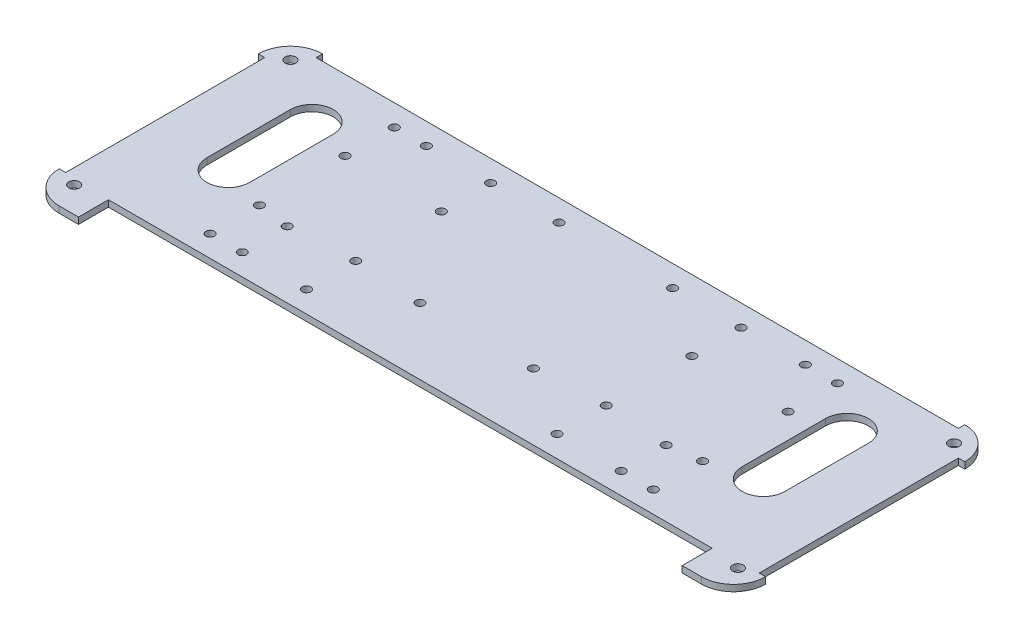
SolidWorks part; units mm, degrees
ref_plane "Plan de face" through (0, 0, 0) normal (0, 0, 1) x (1, 0, 0)
ref_plane "Plan de dessus" through (0, 0, 0) normal (0, 1, 0) x (1, 0, 0)
ref_plane "Plan de droite" through (0, 0, 0) normal (1, 0, 0) x (0, 0, -1)
sketch "Esquisse1" plane through (0, 0, 0) normal (0, 1, 0) x (1, 0, 0)
  line L0 (0, 113) -> (330, 113) construction
  line L1 (0, 0) -> (24, 0)
  line L2 (0, 0) -> (0, 123)
  line L3 (0, 123) -> (330, 123)
  line L4 (330, 0) -> (330, 123)
  line L5 (280, 93) -> (280, 54)
  line L6 (165, 123) -> (165, 0) construction
  line L7 (10, 123) -> (10, 0) construction
  line L8 (24, 0) -> (24, 14)
  line L9 (24, 14) -> (306, 14)
  line L10 (0, 0) -> (330, 0) construction
  line L11 (306, 0) -> (306, 14)
  line L12 (330, 0) -> (306, 0)
  line L13 (30, 93) -> (50, 93) construction
  line L14 (300, 93) -> (300, 54)
  line L15 (30, 93) -> (30, 54)
  line L17 (50, 93) -> (50, 54)
  circle A0 centre (10, 113) radius 2.5
  circle A1 centre (320, 113) radius 2.5
  circle A2 centre (10, 12) radius 2.5
  circle A3 centre (320, 12) radius 2.5
  arc A4 (30, 93) -> (50, 93) centre (40, 93) cw
  arc A5 (30, 54) -> (50, 54) centre (40, 54) ccw
  arc A6 (300, 93) -> (280, 93) centre (290, 93) ccw
  arc A7 (300, 54) -> (280, 54) centre (290, 54) cw
  point P13 (10, 113)
  point P26 (165, 14)
  point P37 (50, 54)
  point P38 (30, 54)
  dimension "D3" = 5
  dimension "D12" = 5
  dimension "D1" = 330
  dimension "D2" = 123
  dimension "D4" = 10
  dimension "D5" = 10
  dimension "D6" = 14
  dimension "D7" = 14
  dimension "D8" = 20
  dimension "D9" = 30
  dimension "D10" = 30
  dimension "D11" = 40
  dimension "D13" = 12
extrude "Extrusion1" add sketch "Esquisse1" along normal blind 3
fillet "Congé1" radius 15 4 edges at (0, 1.5, 0) (330, 1.5, 0) (330, 1.5, -123) (0, 1.5, -123)
sketch "Esquisse2" plane through (0, 3, 0) normal (0, 1, 0) x (1, 0, 0)
  line L0 (0, 120) -> (330, 120) construction
  line L1 (0, 108) -> (0, 15) construction
  line L2 (330, 15) -> (330, 108) construction
  line L3 (3, 123) -> (3, 0) construction
  line L4 (315, 123) -> (15, 123) construction
  line L5 (15, 0) -> (24, 0) construction
  line L6 (165, 123) -> (165, 14) construction
  line L7 (24, 14) -> (306, 14) construction
  line L8 (15, 123) -> (15, 120)
  line L9 (15, 120) -> (315, 120)
  line L10 (0, 108) -> (3, 108)
  line L11 (3, 108) -> (3, 15)
  line L12 (3, 15) -> (0, 15)
  line L13 (0, 15) -> (0, 108)
  line L14 (15, 123) -> (315, 123)
  line L15 (315, 123) -> (315, 120)
  line L16 (330, 15) -> (330, 108)
  line L17 (327, 15) -> (330, 15)
  line L18 (327, 108) -> (327, 15)
  line L19 (330, 108) -> (327, 108)
  point P28 (165, 120)
  dimension "D1" = 3
  dimension "D2" = 3
extrude "Extrusion2" cut sketch "Esquisse2" against normal up to next
sketch "Esquisse3" plane through (0, 3, 0) normal (0, 1, 0) x (1, 0, 0)
  line L0 (165, 120) -> (165, 14) construction
  line L1 (15, 120) -> (315, 120) construction
  line L2 (24, 14) -> (306, 14) construction
  line L3 (50, 67) -> (280, 67) construction
  line L4 (50, 54) -> (50, 93) construction
  line L5 (280, 93) -> (280, 54) construction
  line L6 (61.5, 110) -> (76.5, 110) construction
  line L7 (76.5, 110) -> (76.5, 120) construction
  line L8 (61.5, 87) -> (106.5, 87) construction
  line L9 (61.5, 110) -> (61.5, 87) construction
  line L10 (106.5, 110) -> (106.5, 87) construction
  line L11 (106.5, 110) -> (191.5, 110) construction
  line L12 (191.5, 110) -> (191.5, 45) construction
  line L13 (191.5, 45) -> (61.5, 45) construction
  line L14 (76.5, 110) -> (76.5, 45) construction
  circle A0 centre (76.5, 110) radius 2
  circle A1 centre (253.5, 110) radius 2
  circle A2 centre (76.5, 24) radius 2
  circle A3 centre (253.5, 24) radius 2
  circle A4 centre (61.5, 110) radius 2
  circle A5 centre (106.5, 110) radius 2
  circle A6 centre (61.5, 87) radius 2
  circle A7 centre (106.5, 87) radius 2
  circle A8 centre (61.5, 47) radius 2
  circle A9 centre (106.5, 47) radius 2
  circle A10 centre (106.5, 24) radius 2
  circle A11 centre (61.5, 24) radius 2
  circle A12 centre (223.5, 87) radius 2
  circle A13 centre (223.5, 110) radius 2
  circle A14 centre (268.5, 110) radius 2
  circle A15 centre (268.5, 87) radius 2
  circle A16 centre (268.5, 47) radius 2
  circle A17 centre (268.5, 24) radius 2
  circle A18 centre (223.5, 24) radius 2
  circle A19 centre (223.5, 47) radius 2
  circle A20 centre (191.5, 110) radius 2
  circle A21 centre (191.5, 45) radius 2
  circle A22 centre (138.5, 45) radius 2
  circle A23 centre (138.5, 110) radius 2
  circle A24 centre (76.5, 45) radius 2
  circle A25 centre (253.5, 45) radius 2
  dimension "D1" = 4
  dimension "D2" = 88.5
  dimension "D3" = 10
  dimension "D5" = 15
  dimension "D8" = 130
  dimension "D9" = 65
  dimension "D4" = 43
  dimension "D6" = 45
  dimension "D7" = 23
extrude "Extrusion3" cut sketch "Esquisse3" against normal up to next (3 mm away)
